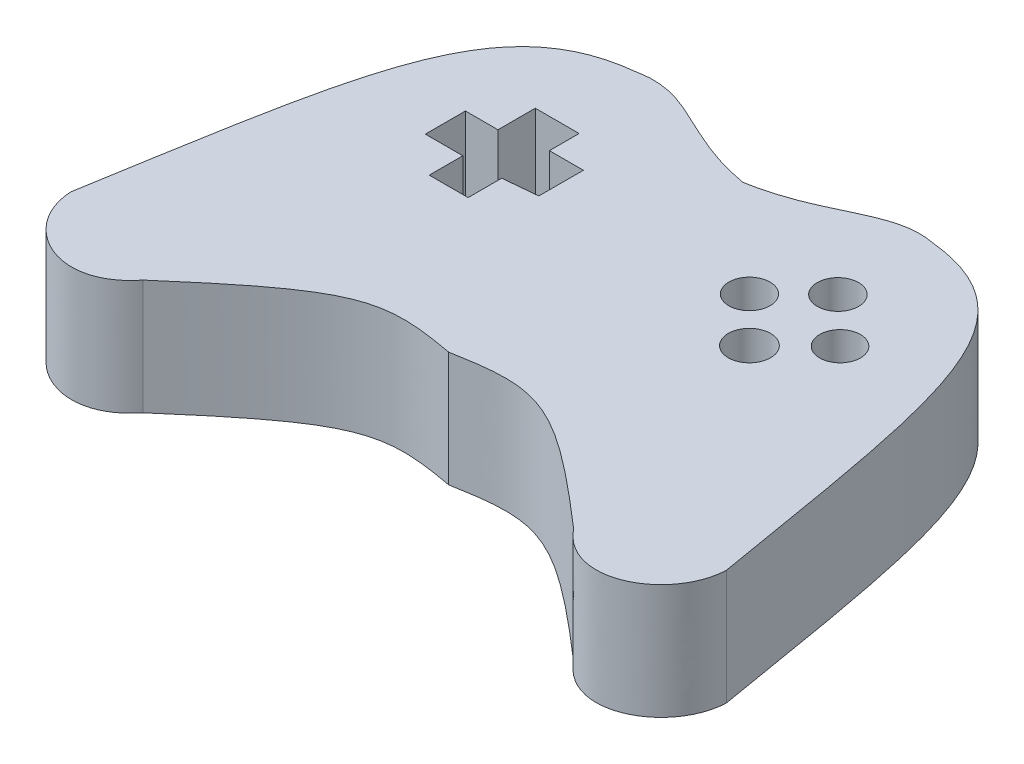
SolidWorks part; units mm, degrees
ref_plane "Front Plane" through (0, 0, 0) normal (0, 0, 1) x (1, 0, 0)
ref_plane "Top Plane" through (0, 0, 0) normal (0, 1, 0) x (1, 0, 0)
ref_plane "Right Plane" through (0, 0, 0) normal (1, 0, 0) x (0, 0, -1)
sketch "Sketch1" plane through (0, 0, 0) normal (0, 1, 0) x (1, 0, 0)
  line L0 (140, 220.5) -> (700, 220.5) construction
  line L1 (0, 0) -> (19.0316, 9.9979) construction
  line L2 (19.0316, 0) -> (0, 9.9979) construction
  line L3 (9.5158, 4.999) -> (9.5158, 9.9979) construction
  line L4 (6.6801, 7.4803) -> (7.3564, 7.4803)
  line L5 (7.3564, 7.4803) -> (7.3564, 6.9638)
  line L6 (7.3564, 6.9638) -> (7.9467, 6.9638)
  line L7 (7.9467, 6.9638) -> (7.9467, 6.189)
  line L8 (7.9467, 6.189) -> (7.3564, 6.1333)
  line L9 (7.3564, 6.1333) -> (7.3564, 5.5496)
  line L10 (7.3564, 5.5496) -> (6.6801, 5.5496)
  line L11 (6.6801, 5.5496) -> (6.6801, 6.1333)
  line L12 (6.6801, 6.1333) -> (6.0283, 6.1333)
  line L13 (6.0283, 6.1333) -> (6.0283, 6.8311)
  line L14 (6.0283, 6.8311) -> (6.594, 6.8311)
  line L15 (6.594, 6.8311) -> (6.594, 7.4803)
  line L16 (6.594, 7.4803) -> (6.6801, 7.4803)
  circle A0 centre (11.2543, 6.5451) radius 0.3581
  circle A1 centre (12.0326, 5.7668) radius 0.368
  circle A2 centre (12.8305, 6.5451) radius 0.3544
  circle A3 centre (12.0326, 7.306) radius 0.36
  spline S0 degree 3 poles (9.5158, 8.169) (8.2771, 8.3842) (7.7837, 9.0759) (6.9383, 8.9068) knots 0 0 0 0 1 1 1 1
  spline S1 degree 3 poles (6.9383, 8.9068) (4.7862, 8.6763) (4.5679, 6.6379) (3.8147, 2.18) knots 0 0 0 0 1 1 1 1
  spline S2 degree 3 poles (3.8147, 2.18) (3.8557, 1.2372) (5.0629, 0.5875) (5.77, 1.479) knots 0 0 0 0 1 1 1 1
  spline S3 degree 3 poles (5.77, 1.479) (7.7838, 3.2314) (8.1541, 3.2991) (9.5158, 3.0531) knots 0 0 0 0 1 1 1 1
  spline S4 degree 3 poles (13.2615, 1.479) (11.2478, 3.2314) (10.8775, 3.2991) (9.5158, 3.0531) knots 0 0 0 0 1 1 1 1
  spline S5 degree 3 poles (15.2169, 2.18) (15.1759, 1.2372) (13.9686, 0.5875) (13.2615, 1.479) knots 0 0 0 0 1 1 1 1
  spline S6 degree 3 poles (12.0933, 8.9068) (14.2454, 8.6763) (14.4637, 6.6379) (15.2169, 2.18) knots 0 0 0 0 1 1 1 1
  spline S7 degree 3 poles (9.5158, 8.169) (10.7545, 8.3842) (11.2479, 9.0759) (12.0933, 8.9068) knots 0 0 0 0 1 1 1 1
extrude "Boss-Extrude1" add sketch "Sketch1" along normal blind 2
